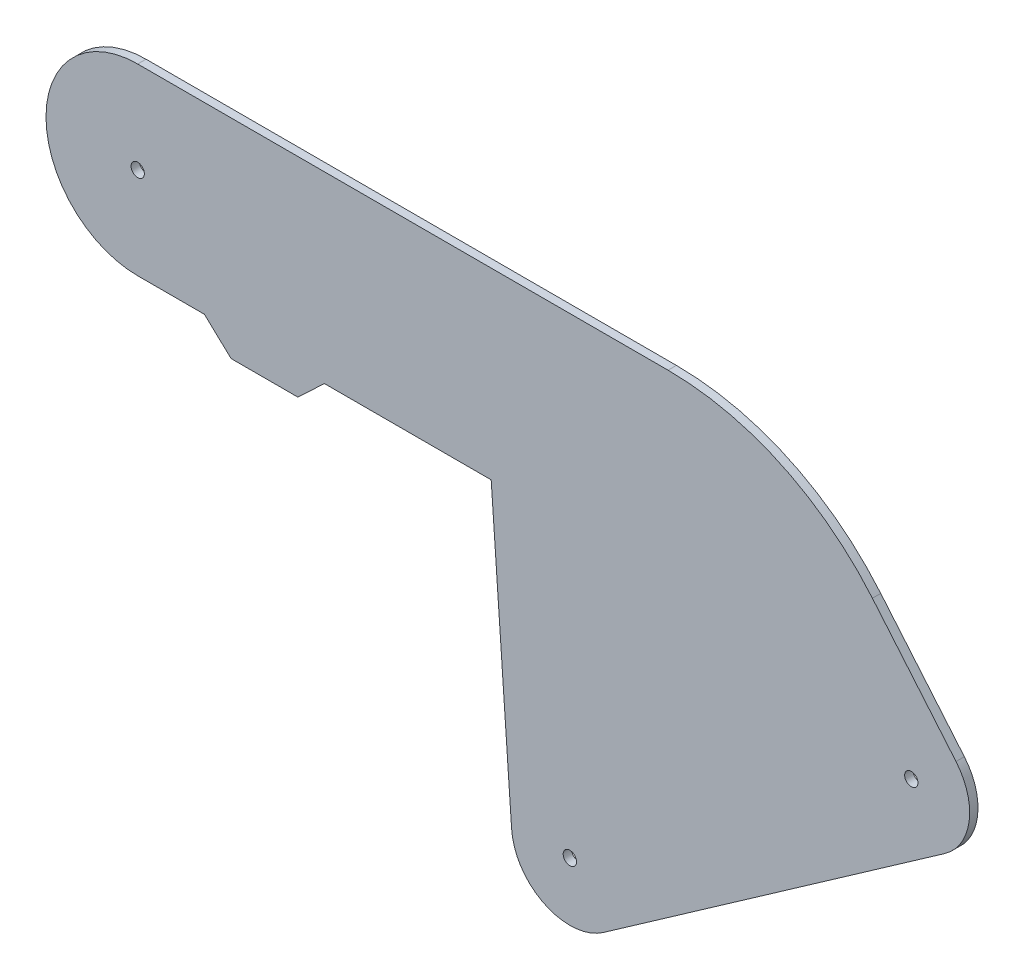
SolidWorks part; units mm, degrees
material "ABS PC"
ref_plane "Front Plane" through (0, 0, 0) normal (0, 0, 1) x (1, 0, 0)
ref_plane "Top Plane" through (0, 0, 0) normal (0, 1, 0) x (1, 0, 0)
ref_plane "Right Plane" through (0, 0, 0) normal (1, 0, 0) x (0, 0, -1)
sketch "Sketch1" plane through (0, 0, 0) normal (0, 0, 1) x (1, 0, 0)
  line L0 (0, 0) -> (0, 215.9) construction
  line L1 (133.35, 0) -> (133.35, 171.45) construction
  line L2 (0.0421, 0) -> (133.3921, 0) construction
  line L3 (50.8, 0) -> (50.8, 123.825) construction
  line L4 (508, 0) -> (508, 50000) construction
  line L11 (133.35, 171.45) -> (0, 171.45) construction
  line L20 (508, 457.2) -> (482.6, 457.2) construction
  line L22 (-203.2, 0) -> (-203.2, 53.1862) construction
  line L31 (-203.2, 520.7) -> (50.8, 520.7) construction
  line L48 (294.6125, 162.3041) -> (164.5721, 71.2488) construction
  line L52 (0, 180.975) -> (134.62, 180.975) construction
  line L53 (134.62, 180.975) -> (142.4012, 69.6985)
  line L62 (177.3198, 53.0432) -> (307.3602, 144.0984)
  line L66 (25.4, 180.975) -> (35.56, 171.45)
  line L67 (35.56, 171.45) -> (60.96, 171.45)
  line L68 (60.96, 171.45) -> (71.12, 180.975)
  line L69 (71.12, 180.975) -> (134.62, 180.975)
  line L70 (0, 250.825) -> (201.9704, 250.825)
  line L71 (279.8005, 214.5322) -> (311.6378, 176.59)
  line L72 (0, 180.975) -> (25.4, 180.975)
  circle A11 centre (508, 75.057) radius 75.057 construction
  arc A19 (0, 250.825) -> (0, 180.975) centre (0, 215.9) ccw
  circle A23 centre (294.6125, 162.3041) radius 2.54
  circle A24 centre (164.5721, 71.2488) radius 2.54
  circle A25 centre (0, 215.9) radius 2.54
  arc A28 (201.9704, 250.825) -> (279.8005, 214.5322) centre (201.9704, 149.225) cw
  circle A29 centre (294.6125, 162.3041) radius 12.7 construction
  arc A32 (311.6378, 176.59) -> (307.3602, 144.0984) centre (294.6125, 162.3041) cw
  circle A33 centre (164.5721, 71.2488) radius 12.7 construction
  arc A34 (142.4012, 69.6985) -> (177.3198, 53.0432) centre (164.5721, 71.2488) ccw
  point P2 (0, 0)
  point P10 (202.806, 253.6406)
  point P17 (-177.8, 889)
  point P18 (0, 0)
  point P27 (177.3198, 53.0432)
  point P38 (201.9704, 250.825)
  point P42 (134.62, 180.975)
  dimension "D4" = 304.8
  dimension "D9" = 49.53
  dimension "D10" = 134.62
  dimension "D11" = 158.75
  dimension "D12" = 59
  dimension "D13" = 150.114
  dimension "D14" = 94
  dimension "D21" = 25.4
  dimension "D3" = 171.45
  dimension "D6" = 130
  dimension "D15" = 25.4
  dimension "D23" = 25.4
  dimension "D8" = 69.85
  dimension "D28" = 5.08
  dimension "D29" = 9.525
  dimension "D30" = 101.6
  dimension "D24" = 22.225
  dimension "D26" = 25.4
  dimension "D1" = 82.55
  dimension "D2" = 215.9
  dimension "D5" = 50.8
  dimension "D7" = 457.2
  dimension "D17" = 457.2
  dimension "D18" = 177.8
  dimension "D19" = 889
  dimension "D20" = 25.4
  dimension "4.5" = 203.2
  dimension "D27" = 63.5
extrude "Boss-Extrude1" add sketch "Sketch1" along normal blind 3.175
